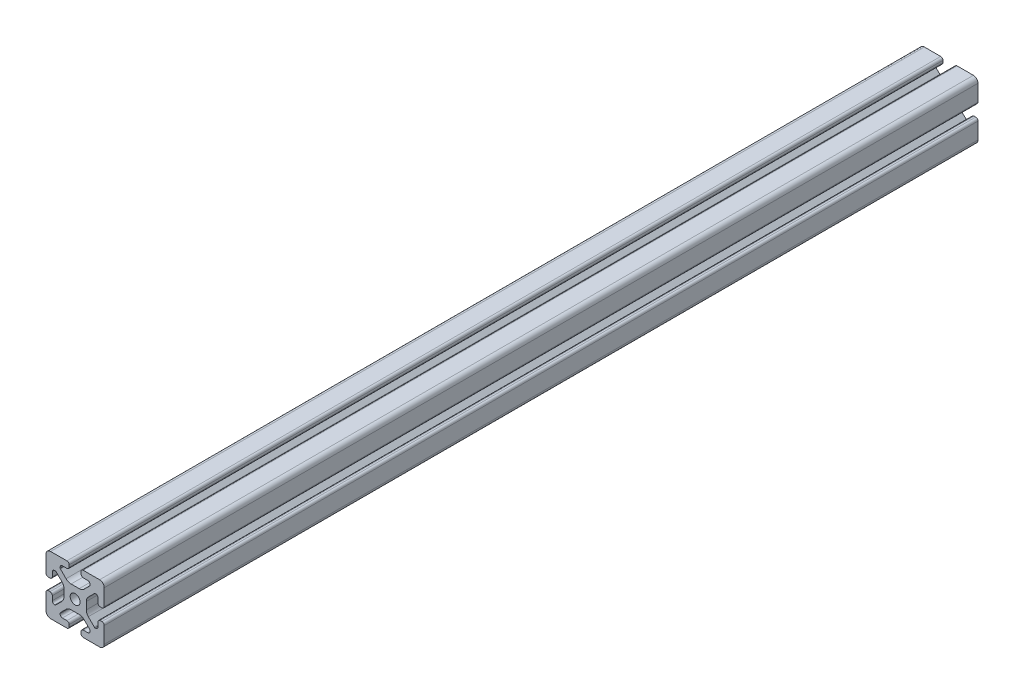
SolidWorks part; units mm, degrees
ref_plane "Front Plane" through (0, 0, 0) normal (0, 0, 1) x (1, 0, 0)
ref_plane "Top Plane" through (0, 0, 0) normal (0, 1, 0) x (1, 0, 0)
ref_plane "Right Plane" through (0, 0, 0) normal (1, 0, 0) x (0, 0, -1)
sketch "Sketch1" plane through (0, 0, 0) normal (0, 0, 1) x (1, 0, 0)
  line L0 (0, 19.7407) -> (0, -19.7407) construction
  line L1 (19.0335, 0) -> (-20.7246, 0) construction
  line L2 (-8.715, -15.5246) -> (-5.63, -15.5246)
  line L3 (-10.285, -13.9546) -> (-10.285, -13.4925)
  line L4 (-6.2171, -9.1098) -> (-10.0624, -12.9551)
  line L5 (2.7773, -7.685) -> (-2.7773, -7.685)
  line L6 (10.0624, -12.9551) -> (6.2171, -9.1098)
  line L7 (10.285, -13.9546) -> (10.285, -13.4925)
  line L8 (5.63, -15.5246) -> (8.715, -15.5246)
  line L9 (4.06, -18.43) -> (4.06, -17.0946)
  line L10 (-4.06, -18.43) -> (-4.06, -17.0946)
  line L11 (15.68, -8.7154) -> (15.68, -5.63)
  line L12 (-14.11, -10.2854) -> (-13.8169, -10.2854)
  line L13 (20, -16.83) -> (20, -5.63)
  line L14 (20, 5.63) -> (20, 13.0011)
  line L15 (-16.83, 20) -> (-5.63, 20)
  line L16 (5.63, 20) -> (12.9796, 20)
  line L17 (-8.715, 15.5246) -> (-5.63, 15.5246)
  line L18 (-20, -17.0184) -> (-20, -5.7579)
  line L19 (-20, 5.573) -> (-20, 13.0045)
  line L20 (-15.68, -8.7154) -> (-15.68, -5.7579)
  line L21 (-16.6746, -20) -> (-5.63, -20)
  line L22 (5.63, -20) -> (13, -20)
  line L23 (14.11, -10.2854) -> (13.6201, -10.2854)
  line L24 (13.1637, -9.947) -> (9.0762, -5.8595)
  line L25 (7.685, -2.5008) -> (7.685, 2.5008)
  line L26 (9.0762, 5.8595) -> (13.2795, 10.0628)
  line L27 (13.8169, 10.2854) -> (14.11, 10.2854)
  line L28 (15.68, 8.7154) -> (15.68, 5.63)
  line L29 (17.25, 4.06) -> (18.43, 4.06)
  line L30 (20, 13.0011) -> (20, 16.83)
  line L31 (16.83, 20) -> (12.9796, 20)
  line L32 (4.06, 18.43) -> (4.06, 17.0946)
  line L33 (5.63, 15.5246) -> (8.715, 15.5246)
  line L34 (10.285, 13.9546) -> (10.285, 13.4925)
  line L35 (10.0624, 12.9551) -> (6.2171, 9.1098)
  line L36 (2.7773, 7.685) -> (-2.7773, 7.685)
  line L37 (-6.2171, 9.1098) -> (-10.0624, 12.9551)
  line L38 (-10.285, 13.4925) -> (-10.285, 13.9546)
  line L39 (-4.06, 17.0946) -> (-4.06, 18.43)
  line L40 (-20, 16.83) -> (-20, 13.0045)
  line L41 (-18.43, 4.003) -> (-17.25, 4.003)
  line L42 (-15.68, 5.573) -> (-15.68, 8.4757)
  line L43 (-14.0552, 10.0447) -> (-13.7199, 10.033)
  line L44 (-13.0405, 9.8238) -> (-9.0762, 5.8595)
  line L45 (-7.685, 2.5008) -> (-7.685, -2.5008)
  line L46 (-9.0762, -5.8595) -> (-13.2795, -10.0628)
  line L47 (-17.2485, -4.1204) -> (-18.43, -4.1204)
  line L48 (13, -20) -> (16.83, -20)
  line L49 (18.43, -4.06) -> (17.25, -4.06)
  arc A0 (-5.63, -15.5246) -> (-4.06, -17.0946) centre (-5.63, -17.0946) cw
  arc A1 (-8.715, -15.5246) -> (-10.285, -13.9546) centre (-8.715, -13.9546) cw
  arc A2 (-10.285, -13.4925) -> (-10.0624, -12.9551) centre (-9.525, -13.4925) cw
  arc A3 (-6.2171, -9.1098) -> (-2.7773, -7.685) centre (-2.7773, -12.5496) cw
  arc A4 (2.7773, -7.685) -> (6.2171, -9.1098) centre (2.7773, -12.5496) cw
  arc A5 (10.0624, -12.9551) -> (10.285, -13.4925) centre (9.525, -13.4925) cw
  arc A6 (10.285, -13.9546) -> (8.715, -15.5246) centre (8.715, -13.9546) cw
  arc A7 (4.06, -17.0946) -> (5.63, -15.5246) centre (5.63, -17.0946) cw
  arc A8 (5.63, -20) -> (4.06, -18.43) centre (5.63, -18.43) cw
  arc A9 (-4.06, -18.43) -> (-5.63, -20) centre (-5.63, -18.43) cw
  circle A10 centre (0, 0) radius 3.4
  arc A11 (17.25, -4.06) -> (15.68, -5.63) centre (17.25, -5.63) ccw
  arc A12 (14.11, -10.2854) -> (15.68, -8.7154) centre (14.11, -8.7154) ccw
  arc A13 (13.1637, -9.947) -> (13.6201, -10.2854) centre (13.8117, -9.55) ccw
  arc A14 (7.685, -2.5008) -> (9.0762, -5.8595) centre (12.435, -2.5008) ccw
  arc A15 (9.0762, 5.8595) -> (7.685, 2.5008) centre (12.435, 2.5008) ccw
  arc A16 (13.8169, 10.2854) -> (13.2795, 10.0628) centre (13.8169, 9.5254) ccw
  arc A17 (15.68, 8.7154) -> (14.11, 10.2854) centre (14.11, 8.7154) ccw
  arc A18 (15.68, 5.63) -> (17.25, 4.06) centre (17.25, 5.63) ccw
  arc A19 (18.43, 4.06) -> (20, 5.63) centre (18.43, 5.63) ccw
  arc A20 (20, 16.83) -> (16.83, 20) centre (16.83, 16.83) ccw
  arc A21 (5.63, 20) -> (4.06, 18.43) centre (5.63, 18.43) ccw
  arc A22 (4.06, 17.0946) -> (5.63, 15.5246) centre (5.63, 17.0946) ccw
  arc A23 (10.285, 13.9546) -> (8.715, 15.5246) centre (8.715, 13.9546) ccw
  arc A24 (10.0624, 12.9551) -> (10.285, 13.4925) centre (9.525, 13.4925) ccw
  arc A25 (2.7773, 7.685) -> (6.2171, 9.1098) centre (2.7773, 12.5496) ccw
  arc A26 (-6.2171, 9.1098) -> (-2.7773, 7.685) centre (-2.7773, 12.5496) ccw
  arc A27 (-10.285, 13.4925) -> (-10.0624, 12.9551) centre (-9.525, 13.4925) ccw
  arc A28 (-8.715, 15.5246) -> (-10.285, 13.9546) centre (-8.715, 13.9546) ccw
  arc A29 (-5.63, 15.5246) -> (-4.06, 17.0946) centre (-5.63, 17.0946) ccw
  arc A30 (-4.06, 18.43) -> (-5.63, 20) centre (-5.63, 18.43) ccw
  arc A31 (-16.83, 20) -> (-20, 16.83) centre (-16.83, 16.83) ccw
  arc A32 (-20, 5.573) -> (-18.43, 4.003) centre (-18.43, 5.573) ccw
  arc A33 (-17.25, 4.003) -> (-15.68, 5.573) centre (-17.25, 5.573) ccw
  arc A34 (-14.0552, 10.0447) -> (-15.68, 8.4757) centre (-14.11, 8.4757) ccw
  arc A35 (-13.0405, 9.8238) -> (-13.7199, 10.033) centre (-13.5779, 9.2864) ccw
  arc A36 (-7.685, 2.5008) -> (-9.0762, 5.8595) centre (-12.435, 2.5008) ccw
  arc A37 (-9.0762, -5.8595) -> (-7.685, -2.5008) centre (-12.435, -2.5008) ccw
  arc A38 (-13.8169, -10.2854) -> (-13.2795, -10.0628) centre (-13.8169, -9.5254) ccw
  arc A39 (-15.68, -8.7154) -> (-14.11, -10.2854) centre (-14.11, -8.7154) ccw
  arc A40 (-15.68, -5.7579) -> (-17.2485, -4.1204) centre (-17.2485, -5.6904) ccw
  arc A41 (-18.43, -4.1204) -> (-20, -5.7579) centre (-18.4315, -5.6904) ccw
  arc A42 (-20, -17.0184) -> (-16.6746, -20) centre (-16.8354, -16.8341) ccw
  arc A43 (16.83, -20) -> (20, -16.83) centre (16.83, -16.83) ccw
  arc A44 (20, -5.63) -> (18.43, -4.06) centre (18.43, -5.63) ccw
  dimension "D1" = 6.8
  dimension "D2" = 4.32
  dimension "D3" = 15.37
  dimension "D4" = 20.57
  dimension "D5" = 15.37
  dimension "D6" = 40
  dimension "D7" = 20
  dimension "D8" = 4.32
  dimension "D9" = 8.12
extrude "Boss-Extrude1" add sketch "Sketch1" along normal blind 600
